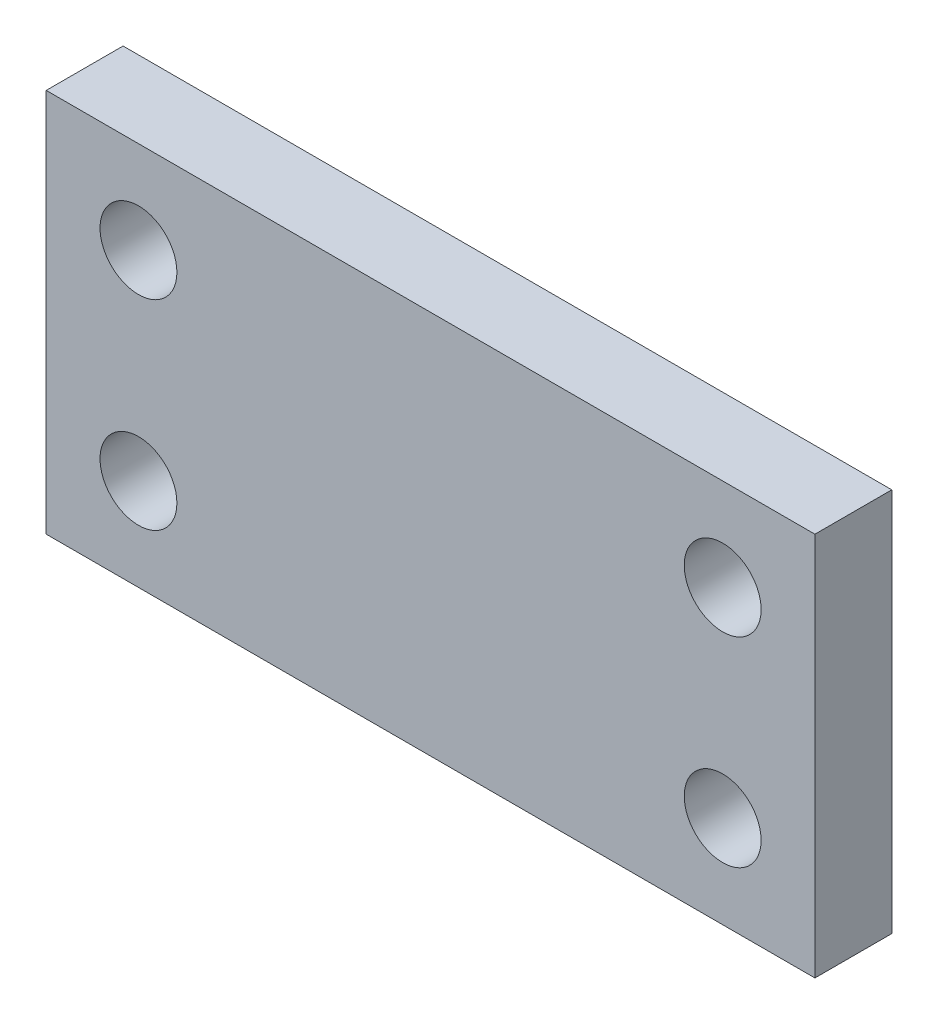
SolidWorks part; units mm, degrees
ref_plane "Alzado" through (0, 0, 0) normal (0, 0, 1) x (1, 0, 0)
ref_plane "Planta" through (0, 0, 0) normal (0, 1, 0) x (1, 0, 0)
ref_plane "Vista lateral" through (0, 0, 0) normal (1, 0, 0) x (0, 0, -1)
sketch "Croquis1" plane through (0, 0, 0) normal (0, 0, 1) x (1, 0, 0)
  line L0 (12, 38) -> (88, 38) construction
  line L1 (0, 0) -> (100, 0)
  line L2 (0, 0) -> (0, 50)
  line L3 (0, 50) -> (100, 50)
  line L4 (100, 0) -> (100, 50)
  line L5 (88, 12) -> (88, 38) construction
  line L6 (12, 12) -> (88, 12) construction
  line L7 (12, 12) -> (12, 38) construction
  circle A0 centre (12, 38) radius 5
  circle A1 centre (12, 12) radius 5
  circle A2 centre (88, 12) radius 5
  circle A3 centre (88, 38) radius 5
  dimension "D4" = 10
  dimension "D1" = 100
  dimension "D2" = 50
  dimension "D3" = 12
extrude "Saliente-Extruir1" add sketch "Croquis1" along normal blind 10
